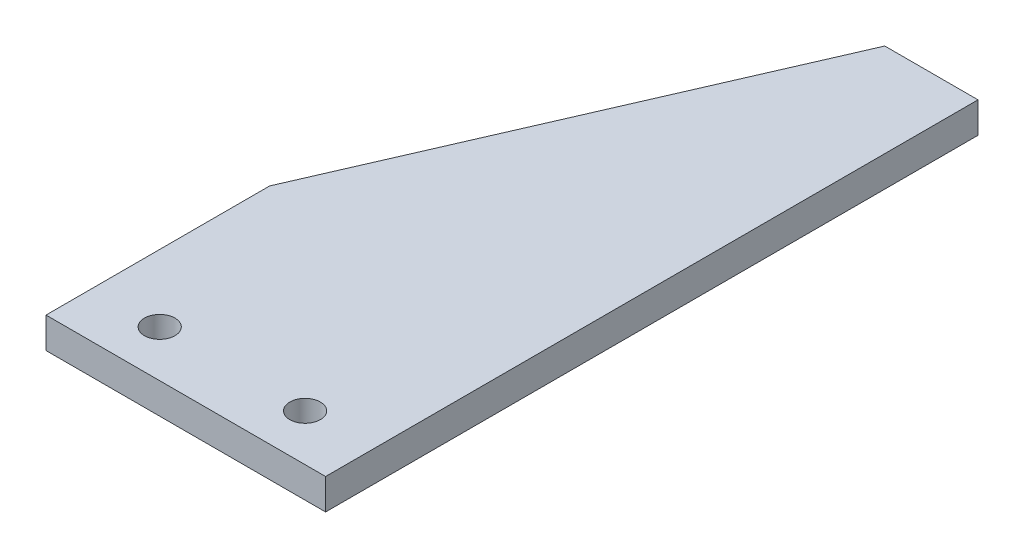
SolidWorks part; units mm, degrees
ref_plane "Front Plane" through (0, 0, 0) normal (0, 0, 1) x (1, 0, 0)
ref_plane "Top Plane" through (0, 0, 0) normal (0, 1, 0) x (1, 0, 0)
ref_plane "Right Plane" through (0, 0, 0) normal (1, 0, 0) x (0, 0, -1)
sketch "Sketch2" plane through (0, 0, 0) normal (0, 1, 0) x (1, 0, 0)
  line L0 (0, 0) -> (0, 30.48)
  line L1 (0, 30.48) -> (25.4, 88.9)
  line L2 (25.4, 88.9) -> (38.1, 88.9)
  line L3 (38.1, 88.9) -> (38.1, 0)
  line L4 (38.1, 0) -> (0, 0)
  circle A0 centre (9.144, 6.35) radius 2.0828
  circle A1 centre (28.956, 6.35) radius 2.0828
  dimension "D5" = 4.1656
  dimension "D6" = 4.1656
  dimension "D7" = 6.35
  dimension "D8" = 6.35
  dimension "D9" = 9.144
  dimension "D10" = 9.144
  dimension "D1" = 88.9
  dimension "D2" = 38.1
  dimension "D3" = 12.7
  dimension "D4" = 30.48
extrude "Boss-Extrude1" add sketch "Sketch2" along normal blind 4.191
